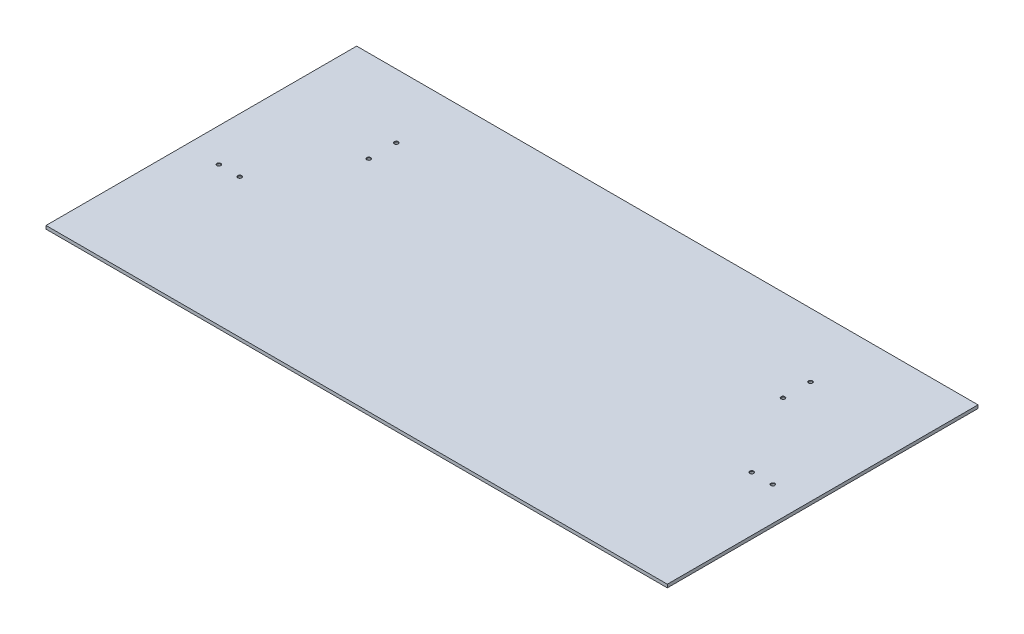
SolidWorks part; units mm, degrees
material "PVC Rigid"
ref_plane "Front Plane" through (0, 0, 0) normal (0, 0, 1) x (1, 0, 0)
ref_plane "Top Plane" through (0, 0, 0) normal (0, 1, 0) x (1, 0, 0)
ref_plane "Right Plane" through (0, 0, 0) normal (1, 0, 0) x (0, 0, -1)
sketch "Sketch1" plane through (0, 0, 0) normal (0, 1, 0) x (1, 0, 0)
  line L1 (0, 0) -> (1219.2, 0)
  line L2 (0, 0) -> (0, 609.6)
  line L3 (0, 609.6) -> (1219.2, 609.6)
  line L4 (1219.2, 0) -> (1219.2, 609.6)
  dimension "D1" = 609.6
  dimension "D2" = 1219.2
extrude "Boss-Extrude1" add sketch "Sketch1" along normal blind 6.35
sketch "Sketch2" plane through (0, 6.35, 0) normal (0, 1, 0) x (1, 0, 0)
  line L0 (203.2, 484.1875) -> (203.2, 430.2125)
  line L1 (1016, 484.1875) -> (1016, 430.2125)
  line L2 (1111.8473, 273.05) -> (1153.1223, 273.05)
  line L3 (66.0777, 273.05) -> (107.3527, 273.05)
  line L4 (203.2, 457.2) -> (1016, 457.2) construction
  line L5 (86.7152, 273.05) -> (609.6, 457.2) construction
  line L6 (609.6, 457.2) -> (1132.4848, 273.05) construction
  line L7 (1219.2, 609.6) -> (0, 609.6) construction
  point P8 (86.7152, 273.05)
  point P13 (1132.4848, 273.05)
  point P17 (0, 0)
  point P20 (609.6, 609.6)
  dimension "D2" = 53.975
  dimension "D1" = 41.275
  dimension "D3" = 184.15
  dimension "32" = 812.8
  dimension "D4" = 1045.7696
  dimension "D5" = 152.4
hole_wizard "1/4 (0.25) Diameter Hole1" positions "Sketch3" profile "Sketch4" hole size "1/4" standard "ANSI Inch" end condition through all
sketch "Sketch3" plane through (0, 6.35, 0) normal (0, 1, 0) x (1, 0, 0)
  point P0 (66.0777, 273.05)
  point P3 (107.3527, 273.05)
  point P6 (203.2, 484.1875)
  point P9 (203.2, 430.2125)
  point P12 (1016, 484.1875)
  point P15 (1016, 430.2125)
  point P18 (1111.8473, 273.05)
  point P21 (1153.1223, 273.05)
sketch "Sketch4" plane through (66.0777, 6.35, -273.05) normal (1, 0, 0) x (0, 0, 1)
  line L0 (0, 0) -> (0, 6.35)
  line L1 (0, 6.35) -> (3.175, 6.35)
  line L2 (3.175, 6.35) -> (3.175, 0.6074)
  line L3 (3.175, 0.6074) -> (3.8989, 0)
  line L5 (3.8989, 0) -> (0, 0)
  line L6 (-3.175, 0.6074) -> (-3.8989, 0) construction
  line L11 (0, -6.35) -> (0, 107.95) construction
  dimension "Thru Hole Dia." = 6.35
  dimension "Thru Hole Depth" = 6.35
  dimension "Near C'Sink Dia." = 7.7978
  dimension "Near C'Sink Angle" = 100
